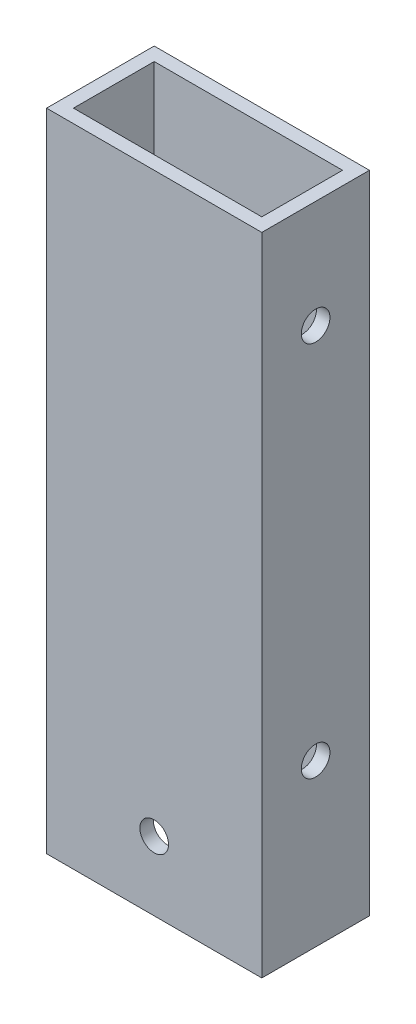
SolidWorks part; units mm, degrees
ref_plane "Front Plane" through (0, 0, 0) normal (0, 0, 1) x (1, 0, 0)
ref_plane "Top Plane" through (0, 0, 0) normal (0, 1, 0) x (1, 0, 0)
ref_plane "Right Plane" through (0, 0, 0) normal (1, 0, 0) x (0, 0, -1)
sketch "Sketch1" plane through (0, 0, 0) normal (0, 1, 0) x (1, 0, 0)
  line L0 (3.175, 3.175) -> (47.625, 3.175)
  line L1 (0, 0) -> (50.8, 0)
  line L2 (0, 0) -> (0, 25.4)
  line L3 (0, 25.4) -> (50.8, 25.4)
  line L4 (50.8, 0) -> (50.8, 25.4)
  line L5 (47.625, 3.175) -> (47.625, 22.225)
  line L6 (3.175, 22.225) -> (47.625, 22.225)
  line L7 (3.175, 3.175) -> (3.175, 22.225)
  dimension "D1" = 50.8
  dimension "D2" = 25.4
  dimension "D3" = 3.175
extrude "Boss-Extrude1" add sketch "Sketch1" along normal blind 152.4
sketch "Sketch2" plane through (0, 0, 0) normal (-1, 0, 0) x (0, 0, 1)
  line L1 (-25.4, 152.4) -> (0, 152.4) construction
  line L2 (-25.4, 0) -> (0, 0) construction
  line L3 (-25.4, 152.4) -> (-25.4, 0) construction
  circle A0 centre (-12.7, 127) radius 3.3782
  circle A1 centre (-12.7, 38.1) radius 3.3782
  dimension "D1" = 6.7564
  dimension "D2" = 6.7564
  dimension "D3" = 25.4
  dimension "D4" = 38.1
  dimension "D5" = 12.7
  dimension "D6" = 12.7
extrude "Cut-Extrude1" cut sketch "Sketch2" against normal through all
sketch "Sketch3" plane through (0, 0, -25.4) normal (0, 0, -1) x (-1, 0, 0)
  circle A0 centre (-25.4, 16.2687) radius 3.3782
  dimension "D1" = 6.7564
extrude "Cut-Extrude2" cut sketch "Sketch3" against normal through all
